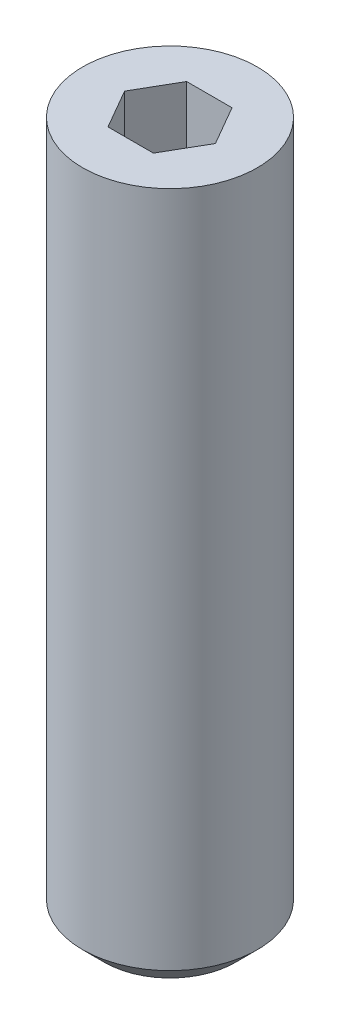
SolidWorks part; units mm, degrees
ref_plane "Front Plane" through (0, 0, 0) normal (0, 0, 1) x (1, 0, 0)
ref_plane "Top Plane" through (0, 0, 0) normal (0, 1, 0) x (1, 0, 0)
ref_plane "Right Plane" through (0, 0, 0) normal (1, 0, 0) x (0, 0, -1)
sketch "Sketch1" plane through (0, 0, 0) normal (0, 1, 0) x (1, 0, 0)
  circle A0 centre (0, 0) radius 1
  dimension "D1" = 2
extrude "Boss-Extrude1" add sketch "Sketch1" along normal blind 8
chamfer "Chamfer1" distance 0.25 angle 45 1 edges at (0, 0, 1)
sketch "Sketch2" plane through (0, 8, 0) normal (0, 1, 0) x (1, 0, 0)
  line L1 (0.2598, -0.45) -> (0.5196, 0)
  line L2 (0.5196, 0) -> (0.2598, 0.45)
  line L3 (0.2598, 0.45) -> (-0.2598, 0.45)
  line L4 (-0.2598, 0.45) -> (-0.5196, 0)
  line L5 (-0.5196, 0) -> (-0.2598, -0.45)
  line L6 (-0.2598, -0.45) -> (0.2598, -0.45)
  circle A0 centre (0, 0) radius 0.45 construction
  dimension "D1" = 0.9
extrude "Cut-Extrude1" cut sketch "Sketch2" against normal blind 0.8
